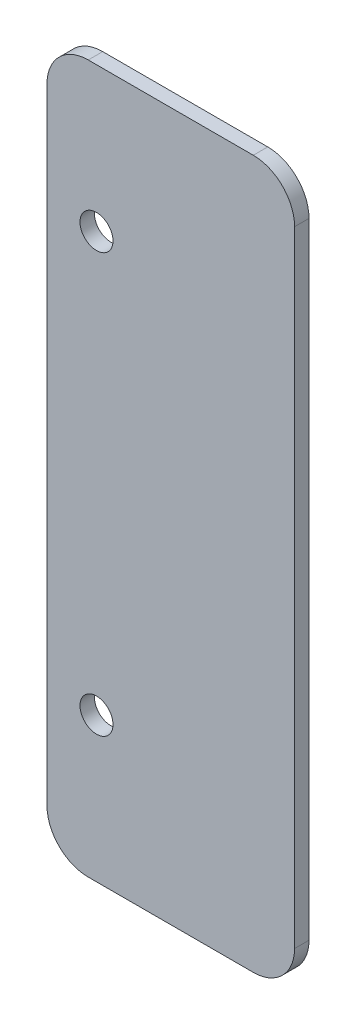
SolidWorks part; units mm, degrees
material "普通碳钢"
ref_plane "前视基准面" through (0, 0, 0) normal (0, 0, 1) x (1, 0, 0)
ref_plane "上视基准面" through (0, 0, 0) normal (0, 1, 0) x (1, 0, 0)
ref_plane "右视基准面" through (0, 0, 0) normal (1, 0, 0) x (0, 0, -1)
sketch "草图1" plane through (0, 0, 0) normal (0, 0, 1) x (1, 0, 0)
  line L1 (2302, -93.75) -> (2362, -93.75)
  line L2 (2302, -93.75) -> (2302, 77.75)
  line L3 (2302, 77.75) -> (2362, 77.75)
  line L4 (2362, -93.75) -> (2362, 77.75)
  circle A0 centre (2342, 85) radius 12.5 construction
  circle A1 centre (2342, -101) radius 12.5 construction
  dimension "D1" = 7.25
  dimension "D2" = 7.25
  dimension "D3" = 20
  dimension "D4" = 60
extrude "凸台-拉伸1" add sketch "草图1" along normal blind 3.5 contours L4 L3 L2 L1
fillet "圆角1" radius 10 4 edges at (2302, -93.75, 1.75) (2362, -93.75, 1.75) (2302, 77.75, 1.75) (2362, 77.75, 1.75)
sketch "草图2" plane through (0, 0, 3.5) normal (0, 0, 1) x (1, 0, 0)
  line L0 (2302, -83.75) -> (2302, 67.75) construction
  line L1 (2312, 77.75) -> (2352, 77.75) construction
  line L2 (2312, -93.75) -> (2352, -93.75) construction
  circle A0 centre (2314, 42.75) radius 4
  circle A1 centre (2314, -58.75) radius 4
  dimension "D1" = 8
  dimension "D2" = 8
  dimension "D3" = 12
  dimension "D4" = 12
  dimension "D5" = 35
  dimension "D6" = 35
extrude "切除-拉伸1" cut sketch "草图2" against normal up to next
